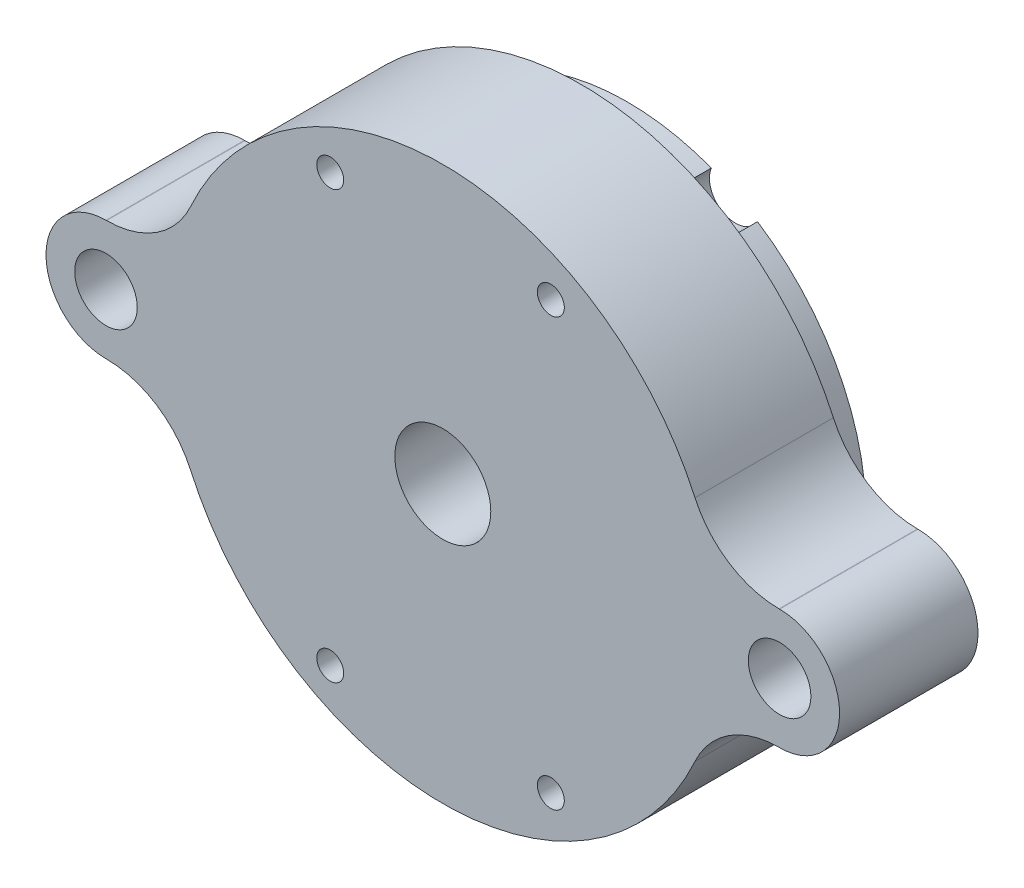
SolidWorks part; units mm, degrees
material "PET"
ref_plane "Front" through (0, 0, 0) normal (0, 0, 1) x (1, 0, 0)
ref_plane "Top" through (0, 0, 0) normal (0, 1, 0) x (1, 0, 0)
ref_plane "Right" through (0, 0, 0) normal (1, 0, 0) x (0, 0, -1)
sketch "Sketch1" plane through (0, 0, 0) normal (0, 0, 1) x (1, 0, 0)
  line L0 (23.1775, 2.8575) -> (16.1706, 2.8575)
  line L1 (23.1775, -2.8575) -> (16.1706, -2.8575)
  line L2 (0, 16.4211) -> (0, -16.4211) construction
  line L3 (-23.1775, -2.8575) -> (-16.1706, -2.8575)
  line L4 (-23.1775, 2.8575) -> (-16.1706, 2.8575)
  circle A0 centre (0, 0) radius 16.4211 construction
  arc A1 (16.1706, 2.8575) -> (-16.1706, 2.8575) centre (0, 0) ccw
  circle A2 centre (0, 0) radius 3.302 construction
  circle A3 centre (0, 0) radius 3.302
  arc A4 (-16.1706, -2.8575) -> (16.1706, -2.8575) centre (0, 0) ccw
  arc A5 (23.1775, -2.8575) -> (23.1775, 2.8575) centre (23.1775, 0) ccw
  arc A6 (23.1775, -2.8575) -> (23.1775, 2.8575) centre (23.1775, 0) ccw
  arc A7 (-23.1775, -2.8575) -> (-23.1775, 2.8575) centre (-23.1775, 0) cw
  arc A8 (-16.1706, 2.8575) -> (-16.1706, -2.8575) centre (0, 0) ccw
  arc A9 (16.1706, 2.8575) -> (16.1706, -2.8575) centre (0, 0) cw
  dimension "D1" = 1.27
extrude "Boss-Extrude1" add sketch "Sketch1" along normal blind 6.35 contours L2 A1 A8 A4 A3 | A1 L2 A3 A4 A9
sketch "Sketch2" plane through (0, 0, 6.35) normal (0, 0, 1) x (1, 0, 0)
  line L4 (23.1775, 4.1275) -> (23.1383, 4.1275)
  line L5 (-23.1383, 4.1275) -> (-23.1775, 4.1275)
  line L6 (-23.1775, -4.1275) -> (-23.1383, -4.1275)
  line L7 (23.1383, -4.1275) -> (23.1775, -4.1275)
  line L8 (23.1775, 4.1275) -> (23.1383, 4.1275)
  line L9 (-23.1383, 4.1275) -> (-23.1775, 4.1275)
  line L10 (-23.1775, -4.1275) -> (-23.1383, -4.1275)
  line L11 (23.1383, -4.1275) -> (23.1775, -4.1275)
  circle A1 centre (0, 0) radius 16.4211
  circle A2 centre (0, 0) radius 16.4211
  arc A8 (17.3537, 7.8581) -> (23.1383, 4.1275) centre (23.1383, 10.4775) ccw
  arc A9 (17.3537, 7.8581) -> (-17.3537, 7.8581) centre (0, 0) ccw
  arc A10 (-23.1383, 4.1275) -> (-17.3537, 7.8581) centre (-23.1383, 10.4775) ccw
  arc A11 (-23.1775, 4.1275) -> (-23.1775, -4.1275) centre (-23.1775, 0) ccw
  arc A12 (-17.3537, -7.8581) -> (-23.1383, -4.1275) centre (-23.1383, -10.4775) ccw
  arc A13 (-17.3537, -7.8581) -> (17.3537, -7.8581) centre (0, 0) ccw
  arc A14 (23.1383, -4.1275) -> (17.3537, -7.8581) centre (23.1383, -10.4775) ccw
  arc A15 (23.1775, -4.1275) -> (23.1775, 4.1275) centre (23.1775, 0) ccw
  arc A16 (17.3537, 7.8581) -> (23.1383, 4.1275) centre (23.1383, 10.4775) ccw
  arc A17 (17.3537, 7.8581) -> (-17.3537, 7.8581) centre (0, 0) ccw
  arc A18 (-23.1383, 4.1275) -> (-17.3537, 7.8581) centre (-23.1383, 10.4775) ccw
  arc A19 (-23.1775, 4.1275) -> (-23.1775, -4.1275) centre (-23.1775, 0) ccw
  arc A20 (-17.3537, -7.8581) -> (-23.1383, -4.1275) centre (-23.1383, -10.4775) ccw
  arc A21 (-17.3537, -7.8581) -> (17.3537, -7.8581) centre (0, 0) ccw
  arc A22 (23.1383, -4.1275) -> (17.3537, -7.8581) centre (23.1383, -10.4775) ccw
  arc A23 (23.1775, -4.1275) -> (23.1775, 4.1275) centre (23.1775, 0) ccw
  dimension "D1" = 0
  dimension "D2" = 0
extrude "Boss-Extrude3" add sketch "Sketch2" against normal blind 3.175 and the other way blind 6.35
hole_wizard "#6 Clearance Hole1" positions "Sketch21" profile "Sketch3" hole size "#6" standard "ANSI Inch" end condition up to next
sketch "Sketch21" plane through (-22.6996, 0.1044, 3.175) normal (0, 0, -1) x (-1, 0, 0)
  point P0 (-45.8771, -0.1044)
  point P3 (0.4779, -0.1044)
sketch "Sketch3" plane through (23.1775, 0, 3.175) normal (1, 0, 0) x (0, 1, 0)
  line L0 (0, 0) -> (0, 9.525)
  line L1 (0, 9.525) -> (2.1526, 9.525)
  line L2 (2.1526, 9.525) -> (2.1526, 0)
  line L5 (2.1526, 0) -> (0, 0)
  line L11 (0, -6.35) -> (0, 107.95) construction
  dimension "Thru Hole Dia." = 4.3053
  dimension "Thru Hole Depth" = 9.525
hole_wizard "#6 Plastic Insert" positions "Sketch4" profile "Sketch5" legacy
sketch "Sketch4" plane through (-45.3006, 0, 3.175) normal (0, 0, -1) x (-1, 0, 0)
  point P0 (-68.4781, 0)
  point P3 (-22.1231, 0)
sketch "Sketch5" plane through (23.1775, 0, 3.175) normal (1, 0, 0) x (0, 1, 0)
  line L0 (0, 0) -> (0, 3.81)
  line L1 (0, 3.81) -> (2.5273, 3.81)
  line L2 (2.5273, 3.81) -> (2.6543, 0)
  line L3 (2.6543, 0) -> (0, 0)
  line L4 (0, 110) -> (0, -10) construction
  dimension "Minor Diameter" = 5.0546
  dimension "Depth" = 3.81
  dimension "Major Diameter" = 5.3086
other "#6 Plastic Insert Hole<1>"
sketch "Sketch22" plane through (0, 0, 12.7) normal (0, 0, 1) x (1, 0, 0)
  circle A0 centre (0, 0) radius 3.302 construction
  circle A1 centre (0, 0) radius 16.4211 construction
  circle A2 centre (0, 0) radius 3.302
  circle A3 centre (0, 0) radius 16.4211
extrude "Boss-Extrude4" add sketch "Sketch22" against normal up to next
hole_wizard "CBORE for #0 Pan Head Machine Screw1" positions "Sketch23" profile "Sketch24" counterbore size "#0" standard "ANSI Inch" end condition through all
sketch "Sketch23" plane through (0, 0, 0) normal (0, 0, -1) x (-1, 0, 0)
  point P0 (-7.435, 14.6946)
  point P2 (7.7474, 14.6946)
  point P4 (7.7474, -14.6946)
  point P6 (-7.435, -14.6946)
  point P9 (-7.435, 14.6946)
  point P10 (7.7474, 14.6946)
  point P11 (-3.6155, 13.2106)
  point P12 (-7.435, 14.6946)
  point P13 (-7.435, -14.6946)
  point P14 (7.7474, -14.6946)
sketch "Sketch24" plane through (7.435, 14.6946, 0) normal (1, 0, 0) x (0, 1, 0)
  line L0 (0, 0) -> (0, 12.7)
  line L1 (0, 12.7) -> (0.9271, 12.7)
  line L3 (0.9271, 12.7) -> (0.9271, 6.35)
  line L4 (0.9271, 6.35) -> (1.7856, 6.35)
  line L5 (1.7856, 6.35) -> (1.7856, 0)
  line L7 (1.7856, 0) -> (0, 0)
  line L11 (0, -6.35) -> (0, 107.95) construction
  dimension "Thru Hole Dia." = 1.8542
  dimension "Thru Hole Depth" = 12.7
  dimension "C'Bore Dia." = 3.5712
  dimension "C'Bore Depth" = 6.35
